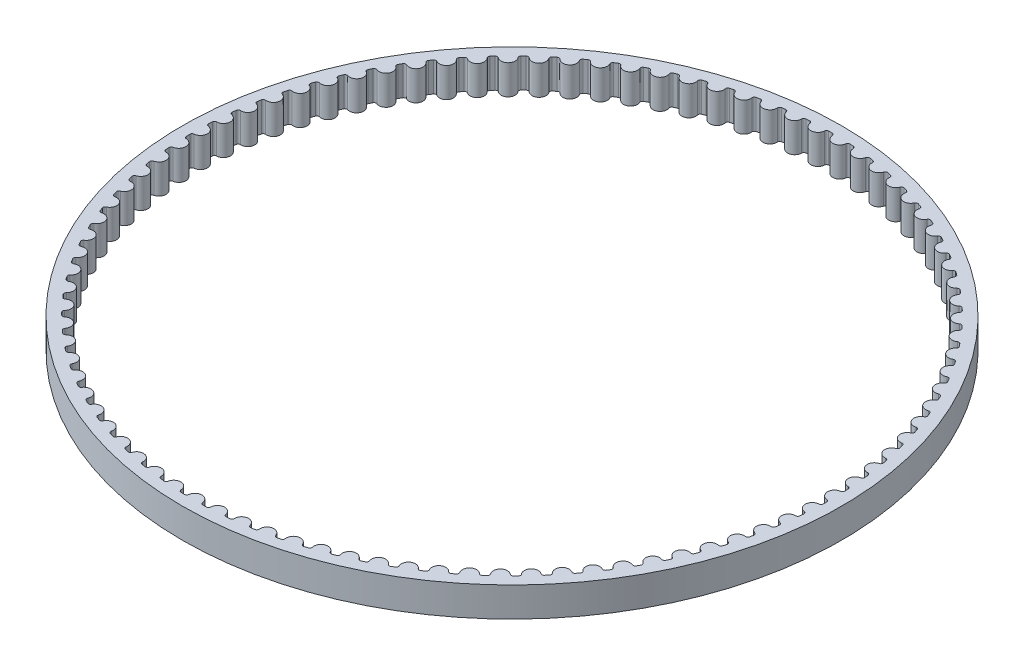
SolidWorks part; units mm, degrees
ref_plane "Front Plane" through (0, 0, 0) normal (0, 0, 1) x (1, 0, 0)
ref_plane "Top Plane" through (0, 0, 0) normal (0, 1, 0) x (1, 0, 0)
ref_plane "Right Plane" through (0, 0, 0) normal (1, 0, 0) x (0, 0, -1)
sketch "Sketch1" plane through (0, 0, 0) normal (0, 1, 0) x (1, 0, 0)
  circle A0 centre (0, 0) radius 44.5683
  arc B0 (-1.7253, -43.0337) -> (-1.2478, -43.0502) centre (0, 0) ccw
  arc B1 (-1.2478, -43.0502) -> (-0.9417, -42.7817) centre (-1.2391, -42.7513) ccw
  arc B2 (0.9417, -42.7817) -> (-0.9417, -42.7817) centre (0, -42.8778) ccw
  arc B3 (0.9417, -42.7817) -> (1.2478, -43.0502) centre (1.2391, -42.7513) ccw
  arc B4 (1.2478, -43.0502) -> (1.7253, -43.0337) centre (0, 0) ccw
  arc B5 (1.7253, -43.0337) -> (2.0121, -42.7447) centre (1.7133, -42.735) ccw
  arc B6 (3.891, -42.6148) -> (2.0121, -42.7447) centre (2.9582, -42.7756) ccw
  arc B7 (3.891, -42.6148) -> (4.2149, -42.8616) centre (4.1856, -42.564) ccw
  arc B8 (4.2149, -42.8616) -> (4.6901, -42.8122) centre (0, 0) ccw
  arc B9 (4.6901, -42.8122) -> (4.9564, -42.5041) centre (4.6575, -42.5149) ccw
  arc B10 (6.8218, -42.2448) -> (4.9564, -42.5041) centre (5.9023, -42.4696) ccw
  arc B11 (6.8218, -42.2448) -> (7.1619, -42.4686) centre (7.1122, -42.1738) ccw
  arc B12 (7.1619, -42.4686) -> (7.6326, -42.3866) centre (0, 0) ccw
  arc B13 (7.6326, -42.3866) -> (7.8769, -42.0608) centre (7.5796, -42.0923) ccw
  arc B14 (9.72, -41.6735) -> (7.8769, -42.0608) centre (8.8182, -41.9612) ccw
  arc B15 (9.72, -41.6735) -> (10.0748, -41.8733) centre (10.0049, -41.5826) ccw
  arc B16 (10.0748, -41.8733) -> (10.5387, -41.759) centre (0, 0) ccw
  arc B17 (10.5387, -41.759) -> (10.76, -41.4172) centre (10.4655, -41.4691) ccw
  arc B18 (12.572, -40.9036) -> (10.76, -41.4172) centre (11.6922, -41.2529) ccw
  arc B19 (12.572, -40.9036) -> (12.9397, -41.0785) centre (12.8499, -40.7933) ccw
  arc B20 (12.9397, -41.0785) -> (13.3946, -40.9324) centre (0, 0) ccw
  arc B21 (13.3946, -40.9324) -> (13.5918, -40.5762) centre (13.3016, -40.6483) ccw
  arc B22 (15.364, -39.9388) -> (13.5918, -40.5762) centre (14.5104, -40.3479) ccw
  arc B23 (15.364, -39.9388) -> (15.7429, -40.0879) centre (15.6336, -39.8096) ccw
  arc B24 (15.7429, -40.0879) -> (16.1867, -39.9108) centre (0, 0) ccw
  arc B25 (16.1867, -39.9108) -> (16.3588, -39.5418) centre (16.0743, -39.6337) ccw
  arc B26 (18.0828, -38.7837) -> (16.3588, -39.5418) centre (17.2595, -39.2507) ccw
  arc B27 (18.0828, -38.7837) -> (18.4711, -38.9062) centre (18.3429, -38.6361) ccw
  arc B28 (18.4711, -38.9062) -> (18.9016, -38.699) centre (0, 0) ccw
  arc B29 (18.9016, -38.699) -> (19.0478, -38.3189) centre (18.7704, -38.4303) ccw
  arc B30 (20.7155, -37.4437) -> (19.0478, -38.3189) centre (19.9263, -37.9664) ccw
  arc B31 (20.7155, -37.4437) -> (21.1113, -37.5392) centre (20.9647, -37.2786) ccw
  arc B32 (21.1113, -37.5392) -> (21.5264, -37.3027) centre (0, 0) ccw
  arc B33 (21.5264, -37.3027) -> (21.6461, -36.9135) centre (21.377, -37.0437) ccw
  arc B34 (23.2494, -35.9253) -> (21.6461, -36.9135) centre (22.4982, -36.5012) ccw
  arc B35 (23.2494, -35.9253) -> (23.6509, -35.9933) centre (23.4867, -35.7434) ccw
  arc B36 (23.6509, -35.9933) -> (24.0487, -35.7287) centre (0, 0) ccw
  arc B37 (24.0487, -35.7287) -> (24.1413, -35.3321) centre (23.8817, -35.4806) ccw
  arc B38 (25.6725, -34.2357) -> (24.1413, -35.3321) centre (24.9628, -34.8621) ccw
  arc B39 (25.6725, -34.2357) -> (26.0777, -34.2758) centre (25.8967, -34.0378) ccw
  arc B40 (26.0777, -34.2758) -> (26.4564, -33.9844) centre (0, 0) ccw
  arc B41 (26.4564, -33.9844) -> (26.5213, -33.5824) centre (26.2727, -33.7485) ccw
  arc B42 (27.9733, -32.3829) -> (26.5213, -33.5824) centre (27.3085, -33.0568) ccw
  arc B43 (27.9733, -32.3829) -> (28.3803, -32.395) centre (28.1833, -32.1701) ccw
  arc B44 (28.3803, -32.395) -> (28.7379, -32.0782) centre (0, 0) ccw
  arc B45 (28.7379, -32.0782) -> (28.775, -31.6727) centre (28.5384, -31.8555) ccw
  arc B46 (30.1408, -30.3759) -> (28.775, -31.6727) centre (29.5241, -31.094) ccw
  arc B47 (30.1408, -30.3759) -> (30.5477, -30.3598) centre (30.3356, -30.1491) ccw
  arc B48 (30.5477, -30.3598) -> (30.8826, -30.0191) centre (0, 0) ccw
  arc B49 (30.8826, -30.0191) -> (30.8916, -29.612) centre (30.6682, -29.8107) ccw
  arc B50 (32.1646, -28.2241) -> (30.8916, -29.612) centre (31.5989, -28.983) ccw
  arc B51 (32.1646, -28.2241) -> (32.5694, -28.18) centre (32.3433, -27.9843) ccw
  arc B52 (32.5694, -28.18) -> (32.88, -27.8169) centre (0, 0) ccw
  arc B53 (32.88, -27.8169) -> (32.861, -27.4102) centre (32.6518, -27.6238) ccw
  arc B54 (34.0352, -25.9377) -> (32.861, -27.4102) centre (33.5232, -26.7339) ccw
  arc B55 (34.0352, -25.9377) -> (34.436, -25.8658) centre (34.1969, -25.6862) ccw
  arc B56 (34.436, -25.8658) -> (34.7208, -25.4822) centre (0, 0) ccw
  arc B57 (34.7208, -25.4822) -> (34.6737, -25.0778) centre (34.4798, -25.3053) ccw
  arc B58 (35.7436, -23.5278) -> (34.6737, -25.0778) centre (35.2877, -24.3574) ccw
  arc B59 (35.7436, -23.5278) -> (36.1385, -23.4284) centre (35.8876, -23.2658) ccw
  arc B60 (36.1385, -23.4284) -> (36.3961, -23.0261) centre (0, 0) ccw
  arc B61 (36.3961, -23.0261) -> (36.3212, -22.6258) centre (36.1435, -22.8662) ccw
  arc B62 (37.2816, -21.0058) -> (36.3212, -22.6258) centre (36.8841, -21.8648) ccw
  arc B63 (37.2816, -21.0058) -> (37.6687, -20.8793) centre (37.4072, -20.7344) ccw
  arc B64 (37.6687, -20.8793) -> (37.898, -20.4602) centre (0, 0) ccw
  arc B65 (37.898, -20.4602) -> (37.7957, -20.0661) centre (37.6349, -20.3182) ccw
  arc B66 (38.642, -18.3836) -> (37.7957, -20.0661) centre (38.3047, -19.268) ccw
  arc B67 (38.642, -18.3836) -> (39.0194, -18.2308) centre (38.7485, -18.1042) ccw
  arc B68 (39.0194, -18.2308) -> (39.2193, -17.7968) centre (0, 0) ccw
  arc B69 (39.2193, -17.7968) -> (39.09, -17.4107) centre (38.947, -17.6733) ccw
  arc B70 (39.8182, -15.6738) -> (39.09, -17.4107) centre (39.5427, -16.5794) ccw
  arc B71 (39.8182, -15.6738) -> (40.1842, -15.4954) centre (39.9053, -15.3878) ccw
  arc B72 (40.1842, -15.4954) -> (40.3537, -15.0486) centre (0, 0) ccw
  arc B73 (40.3537, -15.0486) -> (40.1981, -14.6723) centre (40.0735, -14.9442) ccw
  arc B74 (40.8047, -12.8894) -> (40.1981, -14.6723) centre (40.5924, -13.8118) ccw
  arc B75 (40.8047, -12.8894) -> (41.1575, -12.6861) centre (40.8718, -12.598) ccw
  arc B76 (41.1575, -12.6861) -> (41.2957, -12.2287) centre (0, 0) ccw
  arc B77 (41.2957, -12.2287) -> (41.1145, -11.8641) centre (41.009, -12.1438) ccw
  arc B78 (41.5967, -10.0435) -> (41.1145, -11.8641) centre (41.4485, -10.9784) ccw
  arc B79 (41.5967, -10.0435) -> (41.9347, -9.8163) centre (41.6436, -9.7482) ccw
  arc B80 (41.9347, -9.8163) -> (42.041, -9.3506) centre (0, 0) ccw
  arc B81 (42.041, -9.3506) -> (41.8351, -8.9993) centre (41.7491, -9.2856) ccw
  arc B82 (42.1905, -7.1498) -> (41.8351, -8.9993) centre (42.1072, -8.0927) ccw
  arc B83 (42.1905, -7.1498) -> (42.512, -6.8998) centre (42.2169, -6.8519) ccw
  arc B84 (42.512, -6.8998) -> (42.5859, -6.4278) centre (0, 0) ccw
  arc B85 (42.5859, -6.4278) -> (42.3563, -6.0916) centre (42.2903, -6.3832) ccw
  arc B86 (42.5833, -4.222) -> (42.3563, -6.0916) centre (42.5652, -5.1683) ccw
  arc B87 (42.5833, -4.222) -> (42.8867, -3.9504) centre (42.589, -3.923) ccw
  arc B88 (42.8867, -3.9504) -> (42.9279, -3.4744) centre (0, 0) ccw
  arc B89 (42.9279, -3.4744) -> (42.6756, -3.1548) centre (42.6299, -3.4503) ccw
  arc B90 (42.7731, -1.274) -> (42.6756, -3.1548) centre (42.8203, -2.2194) ccw
  arc B91 (42.7731, -1.274) -> (43.0571, -0.9822) centre (42.7582, -0.9754) ccw
  arc B92 (43.0571, -0.9822) -> (43.0653, -0.5045) centre (0, 0) ccw
  arc B93 (43.0653, -0.5045) -> (42.7916, -0.2031) centre (42.7664, -0.501) ccw
  arc B94 (42.7591, 1.68) -> (42.7916, -0.2031) centre (42.8714, 0.7401) ccw
  arc B95 (42.7591, 1.68) -> (43.0223, 1.9907) centre (42.7236, 1.9769) ccw
  arc B96 (43.0223, 1.9907) -> (42.9975, 2.4678) centre (0, 0) ccw
  arc B97 (42.9975, 2.4678) -> (42.7036, 2.7496) centre (42.699, 2.4507) ccw
  arc B98 (42.5413, 4.626) -> (42.7036, 2.7496) centre (42.7182, 3.6961) ccw
  arc B99 (42.5413, 4.626) -> (42.7824, 4.9541) centre (42.4854, 4.9197) ccw
  arc B100 (42.7824, 4.9541) -> (42.7248, 5.4284) centre (0, 0) ccw
  arc B101 (42.7248, 5.4284) -> (42.4122, 5.6893) centre (42.4282, 5.3907) ccw
  arc B102 (42.1208, 7.5499) -> (42.4122, 5.6893) centre (42.3614, 6.6345) ccw
  arc B103 (42.1208, 7.5499) -> (42.3387, 7.8939) centre (42.0448, 7.8391) ccw
  arc B104 (42.3387, 7.8939) -> (42.2485, 8.3631) centre (0, 0) ccw
  arc B105 (42.2485, 8.3631) -> (41.9186, 8.6018) centre (41.9552, 8.305) ccw
  arc B106 (41.4995, 10.4379) -> (41.9186, 8.6018) centre (41.8028, 9.5412) ccw
  arc B107 (41.4995, 10.4379) -> (41.6932, 10.7961) centre (41.4037, 10.7211) ccw
  arc B108 (41.6932, 10.7961) -> (41.5709, 11.2579) centre (0, 0) ccw
  arc B109 (41.5709, 11.2579) -> (41.2253, 11.4733) centre (41.2823, 11.1798) ccw
  arc B110 (40.6805, 13.2761) -> (41.2253, 11.4733) centre (41.0449, 12.4025) ccw
  arc B111 (40.6805, 13.2761) -> (40.849, 13.6468) centre (40.5654, 13.5521) ccw
  arc B112 (40.849, 13.6468) -> (40.6951, 14.0991) centre (0, 0) ccw
  arc B113 (40.6951, 14.0991) -> (40.3355, 14.2901) centre (40.4126, 14.0012) ccw
  arc B114 (39.6677, 16.0511) -> (40.3355, 14.2901) centre (40.0914, 15.2047) ccw
  arc B115 (39.6677, 16.0511) -> (39.8102, 16.4325) centre (39.5338, 16.3184) ccw
  arc B116 (39.8102, 16.4325) -> (39.6254, 16.8731) centre (0, 0) ccw
  arc B117 (39.6254, 16.8731) -> (39.2535, 17.0389) centre (39.3503, 16.756) ccw
  arc B118 (38.4658, 18.7495) -> (39.2535, 17.0389) centre (38.9469, 17.9344) ccw
  arc B119 (38.4658, 18.7495) -> (38.5816, 19.1399) centre (38.3138, 19.007) ccw
  arc B120 (38.5816, 19.1399) -> (38.3669, 19.5667) centre (0, 0) ccw
  arc B121 (38.3669, 19.5667) -> (37.9844, 19.7064) centre (38.1006, 19.4309) ccw
  arc B122 (37.0806, 21.3587) -> (37.9844, 19.7064) centre (37.6168, 20.5787) ccw
  arc B123 (37.0806, 21.3587) -> (37.1692, 21.7561) centre (36.9112, 21.6051) ccw
  arc B124 (37.1692, 21.7561) -> (36.9256, 22.1671) centre (0, 0) ccw
  arc B125 (36.9256, 22.1671) -> (36.5344, 22.2801) centre (36.6692, 22.0132) ccw
  arc B126 (35.5186, 23.866) -> (36.5344, 22.2801) centre (36.1074, 23.1249) ccw
  arc B127 (35.5186, 23.866) -> (35.5797, 24.2686) centre (35.3327, 24.1001) ccw
  arc B128 (35.5797, 24.2686) -> (35.3083, 24.6618) centre (0, 0) ccw
  arc B129 (35.3083, 24.6618) -> (34.9102, 24.7475) centre (35.0631, 24.4906) ccw
  arc B130 (33.7875, 26.2596) -> (34.9102, 24.7475) centre (34.426, 25.5608) ccw
  arc B131 (33.7875, 26.2596) -> (33.8206, 26.6655) centre (33.5858, 26.4803) ccw
  arc B132 (33.8206, 26.6655) -> (33.5227, 27.039) centre (0, 0) ccw
  arc B133 (33.5227, 27.039) -> (33.1196, 27.097) centre (33.29, 26.8513) ccw
  arc B134 (31.8953, 28.5281) -> (33.1196, 27.097) centre (32.5805, 27.875) ccw
  arc B135 (31.8953, 28.5281) -> (31.9003, 28.9352) centre (31.6788, 28.7344) ccw
  arc B136 (31.9003, 28.9352) -> (31.5774, 29.2873) centre (0, 0) ccw
  arc B137 (31.5774, 29.2873) -> (31.1713, 29.3174) centre (31.3581, 29.084) ccw
  arc B138 (29.8511, 30.6606) -> (31.1713, 29.3174) centre (30.5797, 30.0564) ccw
  arc B139 (29.8511, 30.6606) -> (29.828, 31.0671) centre (29.6209, 30.8515) ccw
  arc B140 (29.828, 31.0671) -> (29.4816, 31.3961) centre (0, 0) ccw
  arc B141 (29.4816, 31.3961) -> (29.0744, 31.3981) centre (29.2769, 31.1782) ccw
  arc B142 (27.6647, 32.647) -> (29.0744, 31.3981) centre (28.4332, 32.0945) ccw
  arc B143 (27.6647, 32.647) -> (27.6136, 33.051) centre (27.4219, 32.8215) ccw
  arc B144 (27.6136, 33.051) -> (27.2453, 33.3553) centre (0, 0) ccw
  arc B145 (27.2453, 33.3553) -> (26.8389, 33.3292) centre (27.0561, 33.1237) ccw
  arc B146 (25.3464, 34.4778) -> (26.8389, 33.3292) centre (26.1513, 33.9797) ccw
  arc B147 (25.3464, 34.4778) -> (25.2676, 34.8773) centre (25.0922, 34.6352) ccw
  arc B148 (25.2676, 34.8773) -> (24.8791, 35.1555) centre (0, 0) ccw
  arc B149 (24.8791, 35.1555) -> (24.4755, 35.1014) centre (24.7064, 34.9114) ccw
  arc B150 (22.9073, 36.1444) -> (24.4755, 35.1014) centre (23.7446, 35.7029) ccw
  arc B151 (22.9073, 36.1444) -> (22.8011, 36.5375) centre (22.6428, 36.2838) ccw
  arc B152 (22.8011, 36.5375) -> (22.3944, 36.7882) centre (0, 0) ccw
  arc B153 (22.3944, 36.7882) -> (21.9955, 36.7064) centre (22.2389, 36.5328) ccw
  arc B154 (20.3591, 37.6386) -> (21.9955, 36.7064) centre (21.2249, 37.256) ccw
  arc B155 (20.3591, 37.6386) -> (20.2261, 38.0235) centre (20.0856, 37.7595) ccw
  arc B156 (20.2261, 38.0235) -> (19.803, 38.2455) centre (0, 0) ccw
  arc B157 (19.803, 38.2455) -> (19.4107, 38.1364) centre (19.6655, 37.98) ccw
  arc B158 (17.7139, 38.9536) -> (19.4107, 38.1364) centre (18.604, 38.6316) ccw
  arc B159 (17.7139, 38.9536) -> (17.5546, 39.3283) centre (17.4327, 39.0553) ccw
  arc B160 (17.5546, 39.3283) -> (17.1172, 39.5206) centre (0, 0) ccw
  arc B161 (17.1172, 39.5206) -> (16.7334, 39.3847) centre (16.9984, 39.2462) ccw
  arc B162 (14.9842, 40.0828) -> (16.7334, 39.3847) centre (15.8944, 39.823) ccw
  arc B163 (14.9842, 40.0828) -> (14.7994, 40.4457) centre (14.6967, 40.1649) ccw
  arc B164 (14.7994, 40.4457) -> (14.3499, 40.6074) centre (0, 0) ccw
  arc B165 (14.3499, 40.6074) -> (13.9763, 40.4453) centre (14.2502, 40.3255) ccw
  arc B166 (12.1832, 41.0211) -> (13.9763, 40.4453) centre (13.1091, 40.8247) ccw
  arc B167 (12.1832, 41.0211) -> (11.9738, 41.3704) centre (11.8907, 41.0831) ccw
  arc B168 (11.9738, 41.3704) -> (11.5141, 41.5006) centre (0, 0) ccw
  arc B169 (11.5141, 41.5006) -> (11.1526, 41.3132) centre (11.4342, 41.2125) ccw
  arc B170 (9.324, 41.7639) -> (11.1526, 41.3132) centre (10.2613, 41.6318) ccw
  arc B171 (9.324, 41.7639) -> (9.0911, 42.0979) centre (9.028, 41.8056) ccw
  arc B172 (9.0911, 42.0979) -> (8.6235, 42.1961) centre (0, 0) ccw
  arc B173 (8.6235, 42.1961) -> (8.2758, 41.9842) centre (8.5636, 41.9032) ccw
  arc B174 (6.4205, 42.3077) -> (8.2758, 41.9842) centre (7.3647, 42.2406) ccw
  arc B175 (6.4205, 42.3077) -> (6.165, 42.6248) centre (6.1222, 42.3288) ccw
  arc B176 (6.165, 42.6248) -> (5.6918, 42.6905) centre (0, 0) ccw
  arc B177 (5.6918, 42.6905) -> (5.3596, 42.4551) centre (5.6523, 42.3942) ccw
  arc B178 (3.4863, 42.6498) -> (5.3596, 42.4551) centre (4.4329, 42.648) ccw
  arc B179 (3.4863, 42.6498) -> (3.2096, 42.9485) centre (3.1873, 42.6504) ccw
  arc B180 (3.2096, 42.9485) -> (2.733, 42.9815) centre (0, 0) ccw
  arc B181 (2.733, 42.9815) -> (2.4178, 42.7237) centre (2.714, 42.6831) ccw
  arc B182 (0.5356, 42.7887) -> (2.4178, 42.7237) centre (1.48, 42.8523) ccw
  arc B183 (0.5356, 42.7887) -> (0.2389, 43.0676) centre (0.2372, 42.7686) ccw
  arc B184 (0.2389, 43.0676) -> (-0.2389, 43.0676) centre (0, 0) ccw
  arc B185 (-0.2389, 43.0676) -> (-0.5356, 42.7887) centre (-0.2372, 42.7686) ccw
  arc B186 (-2.4178, 42.7237) -> (-0.5356, 42.7887) centre (-1.48, 42.8523) ccw
  arc B187 (-2.4178, 42.7237) -> (-2.733, 42.9815) centre (-2.714, 42.6831) ccw
  arc B188 (-2.733, 42.9815) -> (-3.2096, 42.9485) centre (0, 0) ccw
  arc B189 (-3.2096, 42.9485) -> (-3.4863, 42.6498) centre (-3.1873, 42.6504) ccw
  arc B190 (-5.3596, 42.4551) -> (-3.4863, 42.6498) centre (-4.4329, 42.648) ccw
  arc B191 (-5.3596, 42.4551) -> (-5.6918, 42.6905) centre (-5.6523, 42.3942) ccw
  arc B192 (-5.6918, 42.6905) -> (-6.165, 42.6248) centre (0, 0) ccw
  arc B193 (-6.165, 42.6248) -> (-6.4205, 42.3077) centre (-6.1222, 42.3288) ccw
  arc B194 (-8.2758, 41.9842) -> (-6.4205, 42.3077) centre (-7.3647, 42.2406) ccw
  arc B195 (-8.2758, 41.9842) -> (-8.6235, 42.1961) centre (-8.5636, 41.9032) ccw
  arc B196 (-8.6235, 42.1961) -> (-9.0911, 42.0979) centre (0, 0) ccw
  arc B197 (-9.0911, 42.0979) -> (-9.324, 41.7639) centre (-9.028, 41.8056) ccw
  arc B198 (-11.1526, 41.3132) -> (-9.324, 41.7639) centre (-10.2613, 41.6318) ccw
  arc B199 (-11.1526, 41.3132) -> (-11.5141, 41.5006) centre (-11.4342, 41.2125) ccw
  arc B200 (-11.5141, 41.5006) -> (-11.9738, 41.3704) centre (0, 0) ccw
  arc B201 (-11.9738, 41.3704) -> (-12.1832, 41.0211) centre (-11.8907, 41.0831) ccw
  arc B202 (-13.9763, 40.4453) -> (-12.1832, 41.0211) centre (-13.1091, 40.8247) ccw
  arc B203 (-13.9763, 40.4453) -> (-14.3499, 40.6074) centre (-14.2502, 40.3255) ccw
  arc B204 (-14.3499, 40.6074) -> (-14.7994, 40.4457) centre (0, 0) ccw
  arc B205 (-14.7994, 40.4457) -> (-14.9842, 40.0828) centre (-14.6967, 40.1649) ccw
  arc B206 (-16.7334, 39.3847) -> (-14.9842, 40.0828) centre (-15.8944, 39.823) ccw
  arc B207 (-16.7334, 39.3847) -> (-17.1172, 39.5206) centre (-16.9984, 39.2462) ccw
  arc B208 (-17.1172, 39.5206) -> (-17.5546, 39.3283) centre (0, 0) ccw
  arc B209 (-17.5546, 39.3283) -> (-17.7139, 38.9536) centre (-17.4327, 39.0553) ccw
  arc B210 (-19.4107, 38.1364) -> (-17.7139, 38.9536) centre (-18.604, 38.6316) ccw
  arc B211 (-19.4107, 38.1364) -> (-19.803, 38.2455) centre (-19.6655, 37.98) ccw
  arc B212 (-19.803, 38.2455) -> (-20.2261, 38.0235) centre (0, 0) ccw
  arc B213 (-20.2261, 38.0235) -> (-20.3591, 37.6386) centre (-20.0856, 37.7595) ccw
  arc B214 (-21.9955, 36.7064) -> (-20.3591, 37.6386) centre (-21.2249, 37.256) ccw
  arc B215 (-21.9955, 36.7064) -> (-22.3944, 36.7882) centre (-22.2389, 36.5328) ccw
  arc B216 (-22.3944, 36.7882) -> (-22.8011, 36.5375) centre (0, 0) ccw
  arc B217 (-22.8011, 36.5375) -> (-22.9073, 36.1444) centre (-22.6428, 36.2838) ccw
  arc B218 (-24.4755, 35.1014) -> (-22.9073, 36.1444) centre (-23.7446, 35.7029) ccw
  arc B219 (-24.4755, 35.1014) -> (-24.8791, 35.1555) centre (-24.7064, 34.9114) ccw
  arc B220 (-24.8791, 35.1555) -> (-25.2676, 34.8773) centre (0, 0) ccw
  arc B221 (-25.2676, 34.8773) -> (-25.3464, 34.4778) centre (-25.0922, 34.6352) ccw
  arc B222 (-26.8389, 33.3292) -> (-25.3464, 34.4778) centre (-26.1513, 33.9797) ccw
  arc B223 (-26.8389, 33.3292) -> (-27.2453, 33.3553) centre (-27.0561, 33.1237) ccw
  arc B224 (-27.2453, 33.3553) -> (-27.6136, 33.051) centre (0, 0) ccw
  arc B225 (-27.6136, 33.051) -> (-27.6647, 32.647) centre (-27.4219, 32.8215) ccw
  arc B226 (-29.0744, 31.3981) -> (-27.6647, 32.647) centre (-28.4332, 32.0945) ccw
  arc B227 (-29.0744, 31.3981) -> (-29.4816, 31.3961) centre (-29.2769, 31.1782) ccw
  arc B228 (-29.4816, 31.3961) -> (-29.828, 31.0671) centre (0, 0) ccw
  arc B229 (-29.828, 31.0671) -> (-29.8511, 30.6606) centre (-29.6209, 30.8515) ccw
  arc B230 (-31.1713, 29.3174) -> (-29.8511, 30.6606) centre (-30.5797, 30.0564) ccw
  arc B231 (-31.1713, 29.3174) -> (-31.5774, 29.2873) centre (-31.3581, 29.084) ccw
  arc B232 (-31.5774, 29.2873) -> (-31.9003, 28.9352) centre (0, 0) ccw
  arc B233 (-31.9003, 28.9352) -> (-31.8953, 28.5281) centre (-31.6788, 28.7344) ccw
  arc B234 (-33.1196, 27.097) -> (-31.8953, 28.5281) centre (-32.5805, 27.875) ccw
  arc B235 (-33.1196, 27.097) -> (-33.5227, 27.039) centre (-33.29, 26.8513) ccw
  arc B236 (-33.5227, 27.039) -> (-33.8206, 26.6655) centre (0, 0) ccw
  arc B237 (-33.8206, 26.6655) -> (-33.7875, 26.2596) centre (-33.5858, 26.4803) ccw
  arc B238 (-34.9102, 24.7475) -> (-33.7875, 26.2596) centre (-34.426, 25.5608) ccw
  arc B239 (-34.9102, 24.7475) -> (-35.3083, 24.6618) centre (-35.0631, 24.4906) ccw
  arc B240 (-35.3083, 24.6618) -> (-35.5797, 24.2686) centre (0, 0) ccw
  arc B241 (-35.5797, 24.2686) -> (-35.5186, 23.866) centre (-35.3327, 24.1001) ccw
  arc B242 (-36.5344, 22.2801) -> (-35.5186, 23.866) centre (-36.1074, 23.1249) ccw
  arc B243 (-36.5344, 22.2801) -> (-36.9256, 22.1671) centre (-36.6692, 22.0132) ccw
  arc B244 (-36.9256, 22.1671) -> (-37.1692, 21.7561) centre (0, 0) ccw
  arc B245 (-37.1692, 21.7561) -> (-37.0806, 21.3587) centre (-36.9112, 21.6051) ccw
  arc B246 (-37.9844, 19.7064) -> (-37.0806, 21.3587) centre (-37.6168, 20.5787) ccw
  arc B247 (-37.9844, 19.7064) -> (-38.3669, 19.5667) centre (-38.1006, 19.4309) ccw
  arc B248 (-38.3669, 19.5667) -> (-38.5816, 19.1399) centre (0, 0) ccw
  arc B249 (-38.5816, 19.1399) -> (-38.4658, 18.7495) centre (-38.3138, 19.007) ccw
  arc B250 (-39.2535, 17.0389) -> (-38.4658, 18.7495) centre (-38.9469, 17.9344) ccw
  arc B251 (-39.2535, 17.0389) -> (-39.6254, 16.8731) centre (-39.3503, 16.756) ccw
  arc B252 (-39.6254, 16.8731) -> (-39.8102, 16.4325) centre (0, 0) ccw
  arc B253 (-39.8102, 16.4325) -> (-39.6677, 16.0511) centre (-39.5338, 16.3184) ccw
  arc B254 (-40.3355, 14.2901) -> (-39.6677, 16.0511) centre (-40.0914, 15.2047) ccw
  arc B255 (-40.3355, 14.2901) -> (-40.6951, 14.0991) centre (-40.4126, 14.0012) ccw
  arc B256 (-40.6951, 14.0991) -> (-40.849, 13.6468) centre (0, 0) ccw
  arc B257 (-40.849, 13.6468) -> (-40.6805, 13.2761) centre (-40.5654, 13.5521) ccw
  arc B258 (-41.2253, 11.4733) -> (-40.6805, 13.2761) centre (-41.0449, 12.4025) ccw
  arc B259 (-41.2253, 11.4733) -> (-41.5709, 11.2579) centre (-41.2823, 11.1798) ccw
  arc B260 (-41.5709, 11.2579) -> (-41.6932, 10.7961) centre (0, 0) ccw
  arc B261 (-41.6932, 10.7961) -> (-41.4995, 10.4379) centre (-41.4037, 10.7211) ccw
  arc B262 (-41.9186, 8.6018) -> (-41.4995, 10.4379) centre (-41.8028, 9.5412) ccw
  arc B263 (-41.9186, 8.6018) -> (-42.2485, 8.3631) centre (-41.9552, 8.305) ccw
  arc B264 (-42.2485, 8.3631) -> (-42.3387, 7.8939) centre (0, 0) ccw
  arc B265 (-42.3387, 7.8939) -> (-42.1208, 7.5499) centre (-42.0448, 7.8391) ccw
  arc B266 (-42.4122, 5.6893) -> (-42.1208, 7.5499) centre (-42.3614, 6.6345) ccw
  arc B267 (-42.4122, 5.6893) -> (-42.7248, 5.4284) centre (-42.4282, 5.3907) ccw
  arc B268 (-42.7248, 5.4284) -> (-42.7824, 4.9541) centre (0, 0) ccw
  arc B269 (-42.7824, 4.9541) -> (-42.5413, 4.626) centre (-42.4854, 4.9197) ccw
  arc B270 (-42.7036, 2.7496) -> (-42.5413, 4.626) centre (-42.7182, 3.6961) ccw
  arc B271 (-42.7036, 2.7496) -> (-42.9975, 2.4678) centre (-42.699, 2.4507) ccw
  arc B272 (-42.9975, 2.4678) -> (-43.0223, 1.9907) centre (0, 0) ccw
  arc B273 (-43.0223, 1.9907) -> (-42.7591, 1.68) centre (-42.7236, 1.9769) ccw
  arc B274 (-42.7916, -0.2031) -> (-42.7591, 1.68) centre (-42.8714, 0.7401) ccw
  arc B275 (-42.7916, -0.2031) -> (-43.0653, -0.5045) centre (-42.7664, -0.501) ccw
  arc B276 (-43.0653, -0.5045) -> (-43.0571, -0.9822) centre (0, 0) ccw
  arc B277 (-43.0571, -0.9822) -> (-42.7731, -1.274) centre (-42.7582, -0.9754) ccw
  arc B278 (-42.6756, -3.1548) -> (-42.7731, -1.274) centre (-42.8203, -2.2194) ccw
  arc B279 (-42.6756, -3.1548) -> (-42.9279, -3.4744) centre (-42.6299, -3.4503) ccw
  arc B280 (-42.9279, -3.4744) -> (-42.8867, -3.9504) centre (0, 0) ccw
  arc B281 (-42.8867, -3.9504) -> (-42.5833, -4.222) centre (-42.589, -3.923) ccw
  arc B282 (-42.3563, -6.0916) -> (-42.5833, -4.222) centre (-42.5652, -5.1683) ccw
  arc B283 (-42.3563, -6.0916) -> (-42.5859, -6.4278) centre (-42.2903, -6.3832) ccw
  arc B284 (-42.5859, -6.4278) -> (-42.512, -6.8998) centre (0, 0) ccw
  arc B285 (-42.512, -6.8998) -> (-42.1905, -7.1498) centre (-42.2169, -6.8519) ccw
  arc B286 (-41.8351, -8.9993) -> (-42.1905, -7.1498) centre (-42.1072, -8.0927) ccw
  arc B287 (-41.8351, -8.9993) -> (-42.041, -9.3506) centre (-41.7491, -9.2856) ccw
  arc B288 (-42.041, -9.3506) -> (-41.9347, -9.8163) centre (0, 0) ccw
  arc B289 (-41.9347, -9.8163) -> (-41.5967, -10.0435) centre (-41.6436, -9.7482) ccw
  arc B290 (-41.1145, -11.8641) -> (-41.5967, -10.0435) centre (-41.4485, -10.9784) ccw
  arc B291 (-41.1145, -11.8641) -> (-41.2957, -12.2287) centre (-41.009, -12.1438) ccw
  arc B292 (-41.2957, -12.2287) -> (-41.1575, -12.6861) centre (0, 0) ccw
  arc B293 (-41.1575, -12.6861) -> (-40.8047, -12.8894) centre (-40.8718, -12.598) ccw
  arc B294 (-40.1981, -14.6723) -> (-40.8047, -12.8894) centre (-40.5924, -13.8118) ccw
  arc B295 (-40.1981, -14.6723) -> (-40.3537, -15.0486) centre (-40.0735, -14.9442) ccw
  arc B296 (-40.3537, -15.0486) -> (-40.1842, -15.4954) centre (0, 0) ccw
  arc B297 (-40.1842, -15.4954) -> (-39.8182, -15.6738) centre (-39.9053, -15.3878) ccw
  arc B298 (-39.09, -17.4107) -> (-39.8182, -15.6738) centre (-39.5427, -16.5794) ccw
  arc B299 (-39.09, -17.4107) -> (-39.2193, -17.7968) centre (-38.947, -17.6733) ccw
  arc B300 (-39.2193, -17.7968) -> (-39.0194, -18.2308) centre (0, 0) ccw
  arc B301 (-39.0194, -18.2308) -> (-38.642, -18.3836) centre (-38.7485, -18.1042) ccw
  arc B302 (-37.7957, -20.0661) -> (-38.642, -18.3836) centre (-38.3047, -19.268) ccw
  arc B303 (-37.7957, -20.0661) -> (-37.898, -20.4602) centre (-37.6349, -20.3182) ccw
  arc B304 (-37.898, -20.4602) -> (-37.6687, -20.8793) centre (0, 0) ccw
  arc B305 (-37.6687, -20.8793) -> (-37.2816, -21.0058) centre (-37.4072, -20.7344) ccw
  arc B306 (-36.3212, -22.6258) -> (-37.2816, -21.0058) centre (-36.8841, -21.8648) ccw
  arc B307 (-36.3212, -22.6258) -> (-36.3961, -23.0261) centre (-36.1435, -22.8662) ccw
  arc B308 (-36.3961, -23.0261) -> (-36.1385, -23.4284) centre (0, 0) ccw
  arc B309 (-36.1385, -23.4284) -> (-35.7436, -23.5278) centre (-35.8876, -23.2658) ccw
  arc B310 (-34.6737, -25.0778) -> (-35.7436, -23.5278) centre (-35.2877, -24.3574) ccw
  arc B311 (-34.6737, -25.0778) -> (-34.7208, -25.4822) centre (-34.4798, -25.3053) ccw
  arc B312 (-34.7208, -25.4822) -> (-34.436, -25.8658) centre (0, 0) ccw
  arc B313 (-34.436, -25.8658) -> (-34.0352, -25.9377) centre (-34.1969, -25.6862) ccw
  arc B314 (-32.861, -27.4102) -> (-34.0352, -25.9377) centre (-33.5232, -26.7339) ccw
  arc B315 (-32.861, -27.4102) -> (-32.88, -27.8169) centre (-32.6518, -27.6238) ccw
  arc B316 (-32.88, -27.8169) -> (-32.5694, -28.18) centre (0, 0) ccw
  arc B317 (-32.5694, -28.18) -> (-32.1646, -28.2241) centre (-32.3433, -27.9843) ccw
  arc B318 (-30.8916, -29.612) -> (-32.1646, -28.2241) centre (-31.5989, -28.983) ccw
  arc B319 (-30.8916, -29.612) -> (-30.8826, -30.0191) centre (-30.6682, -29.8107) ccw
  arc B320 (-30.8826, -30.0191) -> (-30.5477, -30.3598) centre (0, 0) ccw
  arc B321 (-30.5477, -30.3598) -> (-30.1408, -30.3759) centre (-30.3356, -30.1491) ccw
  arc B322 (-28.775, -31.6727) -> (-30.1408, -30.3759) centre (-29.5241, -31.094) ccw
  arc B323 (-28.775, -31.6727) -> (-28.7379, -32.0782) centre (-28.5384, -31.8555) ccw
  arc B324 (-28.7379, -32.0782) -> (-28.3803, -32.395) centre (0, 0) ccw
  arc B325 (-28.3803, -32.395) -> (-27.9733, -32.3829) centre (-28.1833, -32.1701) ccw
  arc B326 (-26.5213, -33.5824) -> (-27.9733, -32.3829) centre (-27.3085, -33.0568) ccw
  arc B327 (-26.5213, -33.5824) -> (-26.4564, -33.9844) centre (-26.2727, -33.7485) ccw
  arc B328 (-26.4564, -33.9844) -> (-26.0777, -34.2758) centre (0, 0) ccw
  arc B329 (-26.0777, -34.2758) -> (-25.6725, -34.2357) centre (-25.8967, -34.0378) ccw
  arc B330 (-24.1413, -35.3321) -> (-25.6725, -34.2357) centre (-24.9628, -34.8621) ccw
  arc B331 (-24.1413, -35.3321) -> (-24.0487, -35.7287) centre (-23.8817, -35.4806) ccw
  arc B332 (-24.0487, -35.7287) -> (-23.6509, -35.9933) centre (0, 0) ccw
  arc B333 (-23.6509, -35.9933) -> (-23.2494, -35.9253) centre (-23.4867, -35.7434) ccw
  arc B334 (-21.6461, -36.9135) -> (-23.2494, -35.9253) centre (-22.4982, -36.5012) ccw
  arc B335 (-21.6461, -36.9135) -> (-21.5264, -37.3027) centre (-21.377, -37.0437) ccw
  arc B336 (-21.5264, -37.3027) -> (-21.1113, -37.5392) centre (0, 0) ccw
  arc B337 (-21.1113, -37.5392) -> (-20.7155, -37.4437) centre (-20.9647, -37.2786) ccw
  arc B338 (-19.0478, -38.3189) -> (-20.7155, -37.4437) centre (-19.9263, -37.9664) ccw
  arc B339 (-19.0478, -38.3189) -> (-18.9016, -38.699) centre (-18.7704, -38.4303) ccw
  arc B340 (-18.9016, -38.699) -> (-18.4711, -38.9062) centre (0, 0) ccw
  arc B341 (-18.4711, -38.9062) -> (-18.0828, -38.7837) centre (-18.3429, -38.6361) ccw
  arc B342 (-16.3588, -39.5418) -> (-18.0828, -38.7837) centre (-17.2595, -39.2507) ccw
  arc B343 (-16.3588, -39.5418) -> (-16.1867, -39.9108) centre (-16.0743, -39.6337) ccw
  arc B344 (-16.1867, -39.9108) -> (-15.7429, -40.0879) centre (0, 0) ccw
  arc B345 (-15.7429, -40.0879) -> (-15.364, -39.9388) centre (-15.6336, -39.8096) ccw
  arc B346 (-13.5918, -40.5762) -> (-15.364, -39.9388) centre (-14.5104, -40.3479) ccw
  arc B347 (-13.5918, -40.5762) -> (-13.3946, -40.9324) centre (-13.3016, -40.6483) ccw
  arc B348 (-13.3946, -40.9324) -> (-12.9397, -41.0785) centre (0, 0) ccw
  arc B349 (-12.9397, -41.0785) -> (-12.572, -40.9036) centre (-12.8499, -40.7933) ccw
  arc B350 (-10.76, -41.4172) -> (-12.572, -40.9036) centre (-11.6922, -41.2529) ccw
  arc B351 (-10.76, -41.4172) -> (-10.5387, -41.759) centre (-10.4655, -41.4691) ccw
  arc B352 (-10.5387, -41.759) -> (-10.0748, -41.8733) centre (0, 0) ccw
  arc B353 (-10.0748, -41.8733) -> (-9.72, -41.6735) centre (-10.0049, -41.5826) ccw
  arc B354 (-7.8769, -42.0608) -> (-9.72, -41.6735) centre (-8.8182, -41.9612) ccw
  arc B355 (-7.8769, -42.0608) -> (-7.6326, -42.3866) centre (-7.5796, -42.0923) ccw
  arc B356 (-7.6326, -42.3866) -> (-7.1619, -42.4686) centre (0, 0) ccw
  arc B357 (-7.1619, -42.4686) -> (-6.8218, -42.2448) centre (-7.1122, -42.1738) ccw
  arc B358 (-4.9564, -42.5041) -> (-6.8218, -42.2448) centre (-5.9023, -42.4696) ccw
  arc B359 (-4.9564, -42.5041) -> (-4.6901, -42.8122) centre (-4.6575, -42.5149) ccw
  arc B360 (-4.6901, -42.8122) -> (-4.2149, -42.8616) centre (0, 0) ccw
  arc B361 (-4.2149, -42.8616) -> (-3.891, -42.6148) centre (-4.1856, -42.564) ccw
  arc B362 (-2.0121, -42.7447) -> (-3.891, -42.6148) centre (-2.9582, -42.7756) ccw
  arc B363 (-2.0121, -42.7447) -> (-1.7253, -43.0337) centre (-1.7133, -42.735) ccw
  dimension "D1" = 1.5
sketch_block_instance "Block-91T GT2 Pulley-1"
sketch_block "Block-91T GT2 Pulley"
extrude "Boss-Extrude1" add sketch "Sketch1" along normal blind 4
